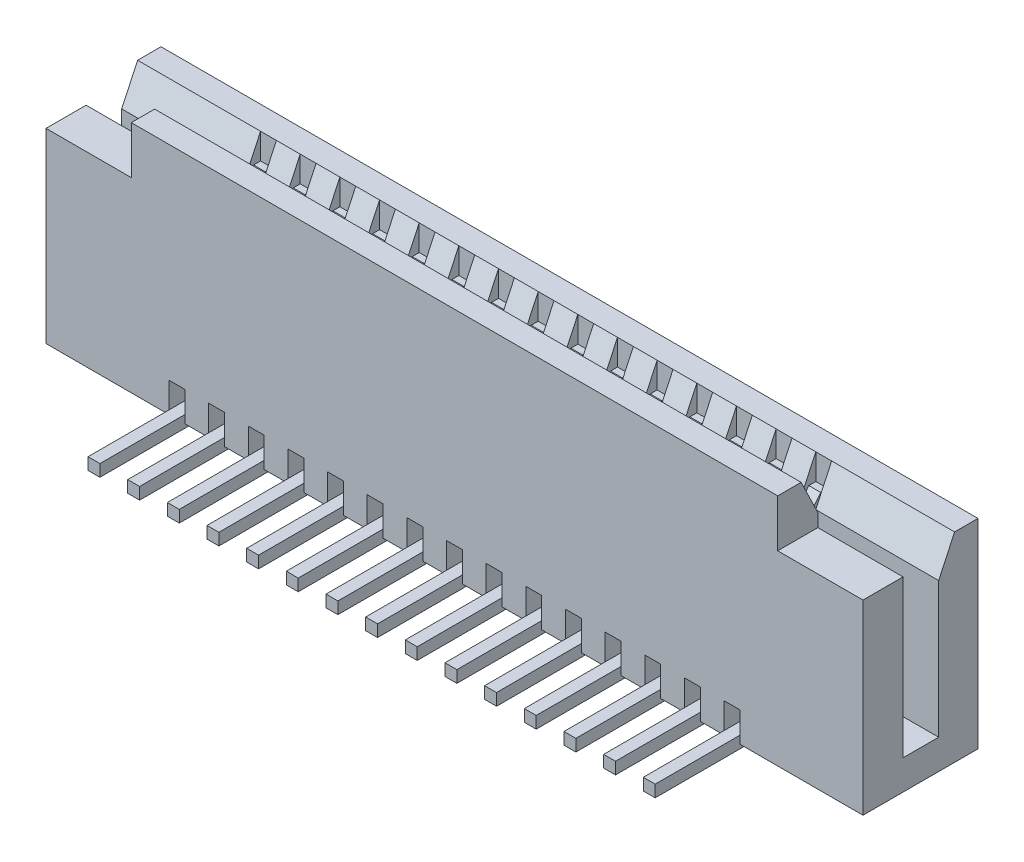
SolidWorks part; units mm, degrees
ref_plane "Front" through (0, 0, 0) normal (0, 0, 1) x (1, 0, 0)
ref_plane "Top" through (0, 0, 0) normal (0, 1, 0) x (1, 0, 0)
ref_plane "Right" through (0, 0, 0) normal (1, 0, 0) x (0, 0, -1)
sketch "Sketch1" plane through (0, 0, 0) normal (0, 1, 0) x (1, 0, 0)
  line L1 (-10.3, 1.45) -> (10.3, 1.45)
  line L2 (-10.3, 1.45) -> (-10.3, -1.45)
  line L3 (-10.3, -1.45) -> (10.3, -1.45)
  line L4 (10.3, 1.45) -> (10.3, -1.45)
  line L5 (-10.3, 1.45) -> (10.3, -1.45) construction
  line L6 (-10.3, -1.45) -> (10.3, 1.45) construction
  point P0 (0, 0)
  dimension "D1" = 2.9
  dimension "D2" = 20.6
extrude "Boss-Extrude1" add sketch "Sketch1" along normal blind 5.9
sketch "Sketch2" plane through (10.3, 0, 0) normal (1, 0, 0) x (0, 0, -1)
  line L1 (-1.45, 5.9) -> (1.45, 5.9) construction
  line L2 (-0.8599, 5.9) -> (-0.439, 5.0322)
  line L3 (-0.439, 5.0322) -> (1.45, 5.0322)
  line L4 (1.45, 5.9) -> (1.45, 0) construction
  line L5 (1.45, 5.0322) -> (1.45, 5.9)
  line L6 (1.45, 5.9) -> (-0.8599, 5.9)
extrude "Cut-Extrude1" cut sketch "Sketch2" against normal through all
sketch "Sketch3" plane through (0, 0, 0) normal (0, -1, 0) x (1, 0, 0)
  line L1 (-7.2, 2.7023) -> (-6.8, 2.7023)
  line L2 (-7.2, 2.7023) -> (-7.2, -4.1616)
  line L3 (-7.2, -4.1616) -> (-6.8, -4.1616)
  line L4 (-6.8, 2.7023) -> (-6.8, -4.1616)
  line L5 (-10.3, -1.45) -> (-10.3, 1.45) construction
  line L6 (-6.2, 2.7023) -> (-5.8, 2.7023)
  line L7 (-6.2, 2.7023) -> (-6.2, -4.1616)
  line L8 (-6.2, -4.1616) -> (-5.8, -4.1616)
  line L9 (-5.8, 2.7023) -> (-5.8, -4.1616)
  line L10 (-5.2, 2.7023) -> (-4.8, 2.7023)
  line L11 (-5.2, 2.7023) -> (-5.2, -4.1616)
  line L12 (-5.2, -4.1616) -> (-4.8, -4.1616)
  line L13 (-4.8, 2.7023) -> (-4.8, -4.1616)
  line L14 (-4.2, 2.7023) -> (-3.8, 2.7023)
  line L15 (-4.2, 2.7023) -> (-4.2, -4.1616)
  line L16 (-4.2, -4.1616) -> (-3.8, -4.1616)
  line L17 (-3.8, 2.7023) -> (-3.8, -4.1616)
  line L18 (-3.2, 2.7023) -> (-2.8, 2.7023)
  line L19 (-3.2, 2.7023) -> (-3.2, -4.1616)
  line L20 (-3.2, -4.1616) -> (-2.8, -4.1616)
  line L21 (-2.8, 2.7023) -> (-2.8, -4.1616)
  line L22 (-2.2, 2.7023) -> (-1.8, 2.7023)
  line L23 (-2.2, 2.7023) -> (-2.2, -4.1616)
  line L24 (-2.2, -4.1616) -> (-1.8, -4.1616)
  line L25 (-1.8, 2.7023) -> (-1.8, -4.1616)
  line L26 (-1.2, 2.7023) -> (-0.8, 2.7023)
  line L27 (-1.2, 2.7023) -> (-1.2, -4.1616)
  line L28 (-1.2, -4.1616) -> (-0.8, -4.1616)
  line L29 (-0.8, 2.7023) -> (-0.8, -4.1616)
  line L30 (-0.2, 2.7023) -> (0.2, 2.7023)
  line L31 (-0.2, 2.7023) -> (-0.2, -4.1616)
  line L32 (-0.2, -4.1616) -> (0.2, -4.1616)
  line L33 (0.2, 2.7023) -> (0.2, -4.1616)
  line L34 (0.8, 2.7023) -> (1.2, 2.7023)
  line L35 (0.8, 2.7023) -> (0.8, -4.1616)
  line L36 (0.8, -4.1616) -> (1.2, -4.1616)
  line L37 (1.2, 2.7023) -> (1.2, -4.1616)
  line L38 (1.8, 2.7023) -> (2.2, 2.7023)
  line L39 (1.8, 2.7023) -> (1.8, -4.1616)
  line L40 (1.8, -4.1616) -> (2.2, -4.1616)
  line L41 (2.2, 2.7023) -> (2.2, -4.1616)
  line L42 (2.8, 2.7023) -> (3.2, 2.7023)
  line L43 (2.8, 2.7023) -> (2.8, -4.1616)
  line L44 (2.8, -4.1616) -> (3.2, -4.1616)
  line L45 (3.2, 2.7023) -> (3.2, -4.1616)
  line L46 (3.8, 2.7023) -> (4.2, 2.7023)
  line L47 (3.8, 2.7023) -> (3.8, -4.1616)
  line L48 (3.8, -4.1616) -> (4.2, -4.1616)
  line L49 (4.2, 2.7023) -> (4.2, -4.1616)
  line L50 (4.8, 2.7023) -> (5.2, 2.7023)
  line L51 (4.8, 2.7023) -> (4.8, -4.1616)
  line L52 (4.8, -4.1616) -> (5.2, -4.1616)
  line L53 (5.2, 2.7023) -> (5.2, -4.1616)
  line L54 (5.8, 2.7023) -> (6.2, 2.7023)
  line L55 (5.8, 2.7023) -> (5.8, -4.1616)
  line L56 (5.8, -4.1616) -> (6.2, -4.1616)
  line L57 (6.2, 2.7023) -> (6.2, -4.1616)
  line L58 (6.8, 2.7023) -> (7.2, 2.7023)
  line L59 (6.8, 2.7023) -> (6.8, -4.1616)
  line L60 (6.8, -4.1616) -> (7.2, -4.1616)
  line L61 (7.2, 2.7023) -> (7.2, -4.1616)
  dimension "D1" = 0.4
  dimension "D2" = 3.1
  dimension "D3" = 15
sketch "Sketch4" plane through (-10.3, 0, 0) normal (-1, 0, 0) x (0, 0, 1)
  line L0 (-0.4585, 4.1712) -> (0.439, 4.1712)
  line L1 (-0.86, 5.0322) -> (-0.4585, 4.1712)
  line L2 (0.439, 5.0322) -> (-1.45, 5.0322) construction
  line L3 (0.439, 5.0322) -> (0.439, 4.1712)
  dimension "D1" = 0.59
  dimension "D2" = 115
  dimension "D3" = 0.95
extrude "Cut-Extrude2" cut sketch "Sketch4" against normal through all and the other way through all
sketch "Sketch5" plane through (0, 4.1712, 0) normal (0, 1, 0) x (1, 0, 0)
  line L1 (-10.3, 0.4585) -> (10.3, 0.4585)
  line L2 (-10.3, 0.4585) -> (-10.3, -0.439)
  line L3 (-10.3, -0.439) -> (10.3, -0.439)
  line L4 (10.3, 0.4585) -> (10.3, -0.439)
extrude "Cut-Extrude3" cut sketch "Sketch5" against normal offset from surface (3.4212 mm away) 0.75 up to face at (0, 0, 0)
extrude "Cut-Extrude4" cut sketch "Sketch3" against normal blind 0.75
sketch "Sketch6" plane through (0, 5.9, 0) normal (0, 1, 0) x (1, 0, 0)
  line L0 (-10.3, -0.8599) -> (10.3, -0.8599) construction
  line L1 (-7.2, -0.8599) -> (-6.8, -0.8599)
  line L2 (-7.2, -0.8599) -> (-7.2, 0.86)
  line L3 (-7.2, 0.86) -> (-6.8, 0.86)
  line L4 (-6.8, -0.8599) -> (-6.8, 0.86)
  line L5 (-7.2, 0.4585) -> (-7.2, -0.439) construction
  line L6 (-6.2, -0.8599) -> (-5.8, -0.8599)
  line L7 (-6.2, -0.8599) -> (-6.2, 0.86)
  line L8 (-6.2, 0.86) -> (-5.8, 0.86)
  line L9 (-5.8, -0.8599) -> (-5.8, 0.86)
  line L10 (-5.2, -0.8599) -> (-4.8, -0.8599)
  line L11 (-5.2, -0.8599) -> (-5.2, 0.86)
  line L12 (-5.2, 0.86) -> (-4.8, 0.86)
  line L13 (-4.8, -0.8599) -> (-4.8, 0.86)
  line L14 (-4.2, -0.8599) -> (-3.8, -0.8599)
  line L15 (-4.2, -0.8599) -> (-4.2, 0.86)
  line L16 (-4.2, 0.86) -> (-3.8, 0.86)
  line L17 (-3.8, -0.8599) -> (-3.8, 0.86)
  line L18 (-3.2, -0.8599) -> (-2.8, -0.8599)
  line L19 (-3.2, -0.8599) -> (-3.2, 0.86)
  line L20 (-3.2, 0.86) -> (-2.8, 0.86)
  line L21 (-2.8, -0.8599) -> (-2.8, 0.86)
  line L22 (-2.2, -0.8599) -> (-1.8, -0.8599)
  line L23 (-2.2, -0.8599) -> (-2.2, 0.86)
  line L24 (-2.2, 0.86) -> (-1.8, 0.86)
  line L25 (-1.8, -0.8599) -> (-1.8, 0.86)
  line L26 (-1.2, -0.8599) -> (-0.8, -0.8599)
  line L27 (-1.2, -0.8599) -> (-1.2, 0.86)
  line L28 (-1.2, 0.86) -> (-0.8, 0.86)
  line L29 (-0.8, -0.8599) -> (-0.8, 0.86)
  line L30 (-0.2, -0.8599) -> (0.2, -0.8599)
  line L31 (-0.2, -0.8599) -> (-0.2, 0.86)
  line L32 (-0.2, 0.86) -> (0.2, 0.86)
  line L33 (0.2, -0.8599) -> (0.2, 0.86)
  line L34 (0.8, -0.8599) -> (1.2, -0.8599)
  line L35 (0.8, -0.8599) -> (0.8, 0.86)
  line L36 (0.8, 0.86) -> (1.2, 0.86)
  line L37 (1.2, -0.8599) -> (1.2, 0.86)
  line L38 (1.8, -0.8599) -> (2.2, -0.8599)
  line L39 (1.8, -0.8599) -> (1.8, 0.86)
  line L40 (1.8, 0.86) -> (2.2, 0.86)
  line L41 (2.2, -0.8599) -> (2.2, 0.86)
  line L42 (2.8, -0.8599) -> (3.2, -0.8599)
  line L43 (2.8, -0.8599) -> (2.8, 0.86)
  line L44 (2.8, 0.86) -> (3.2, 0.86)
  line L45 (3.2, -0.8599) -> (3.2, 0.86)
  line L46 (3.8, -0.8599) -> (4.2, -0.8599)
  line L47 (3.8, -0.8599) -> (3.8, 0.86)
  line L48 (3.8, 0.86) -> (4.2, 0.86)
  line L49 (4.2, -0.8599) -> (4.2, 0.86)
  line L50 (4.8, -0.8599) -> (5.2, -0.8599)
  line L51 (4.8, -0.8599) -> (4.8, 0.86)
  line L52 (4.8, 0.86) -> (5.2, 0.86)
  line L53 (5.2, -0.8599) -> (5.2, 0.86)
  line L54 (5.8, -0.8599) -> (6.2, -0.8599)
  line L55 (5.8, -0.8599) -> (5.8, 0.86)
  line L56 (5.8, 0.86) -> (6.2, 0.86)
  line L57 (6.2, -0.8599) -> (6.2, 0.86)
  line L58 (6.8, -0.8599) -> (7.2, -0.8599)
  line L59 (6.8, -0.8599) -> (6.8, 0.86)
  line L60 (6.8, 0.86) -> (7.2, 0.86)
  line L61 (7.2, -0.8599) -> (7.2, 0.86)
  line L62 (10.3, 0.86) -> (-10.3, 0.86) construction
  dimension "D1" = 15
extrude "Cut-Extrude5" cut sketch "Sketch6" against normal through all
ref_plane "Plane1" through (7, 0, 0) normal (1, 0, 0) x (0, 0, -1)
sketch "Sketch8" plane through (7, 0, 0) normal (1, 0, 0) x (0, 0, -1)
  line L0 (2.3243, 0) -> (0.6185, 0)
  line L1 (0.6185, 0) -> (0.6185, 4.1712)
  line L2 (0.6185, 4.1712) -> (0.7067, 4.2829)
  line L3 (0.7067, 4.2829) -> (0.8103, 4.2829)
  line L4 (0.4585, 0.75) -> (0.4585, 4.1712) construction
  dimension "D1" = 0.16
surface "Surface-Extrude1" sketch "Sketch8" parameters "D1"=0.3
thicken "Thicken1" surfaces to thicken 107 thickness 0.15 thickness side both sides parameters "D1"=0.15
pattern_linear "LPattern3" count 15 spacing 1 along (-1, 0, 0) of bodies 108
sketch "Sketch9" plane through (7, 0, 0) normal (1, 0, 0) x (0, 0, -1)
  line L0 (-3.54, 0) -> (-0.5176, 0)
  line L2 (-0.5176, 0) -> (-0.5176, 4.3678)
  line L5 (-0.5176, 4.3678) -> (-0.175, 4.7857)
  line L9 (-1.45, 0) -> (1.45, 0) construction
  line L10 (-0.175, 4.7857) -> (-0.2752, 5.0322)
  line L11 (-0.2752, 5.0322) -> (-0.7182, 5.0322)
surface "Surface-Extrude2" sketch "Sketch9" parameters "D1"=0.3
thicken "Thicken2" surfaces to thicken 128 thickness 0.15 thickness side both sides parameters "D1"=0.15
pattern_linear "LPattern4" count 15 spacing 1 along (-1, 0, 0) of bodies 129
sketch "Sketch10" plane through (0, 0, 1.45) normal (0, 0, 1) x (1, 0, 0)
  line L0 (0, 0) -> (0, -50000) construction
  line L1 (-10.3, 5.9) -> (-8.15, 5.9)
  line L2 (-10.3, 5.9) -> (-10.3, 4.7)
  line L3 (-10.3, 4.7) -> (-8.15, 4.7)
  line L4 (-8.15, 5.9) -> (-8.15, 4.7)
  line L5 (8.15, 5.9) -> (8.15, 4.7)
  line L6 (10.3, 4.7) -> (8.15, 4.7)
  line L7 (10.3, 5.9) -> (10.3, 4.7)
  line L8 (10.3, 5.9) -> (8.15, 5.9)
  dimension "D1" = 2.15
  dimension "D2" = 1.2
extrude "Cut-Extrude6" cut sketch "Sketch10" against normal blind 1.2
